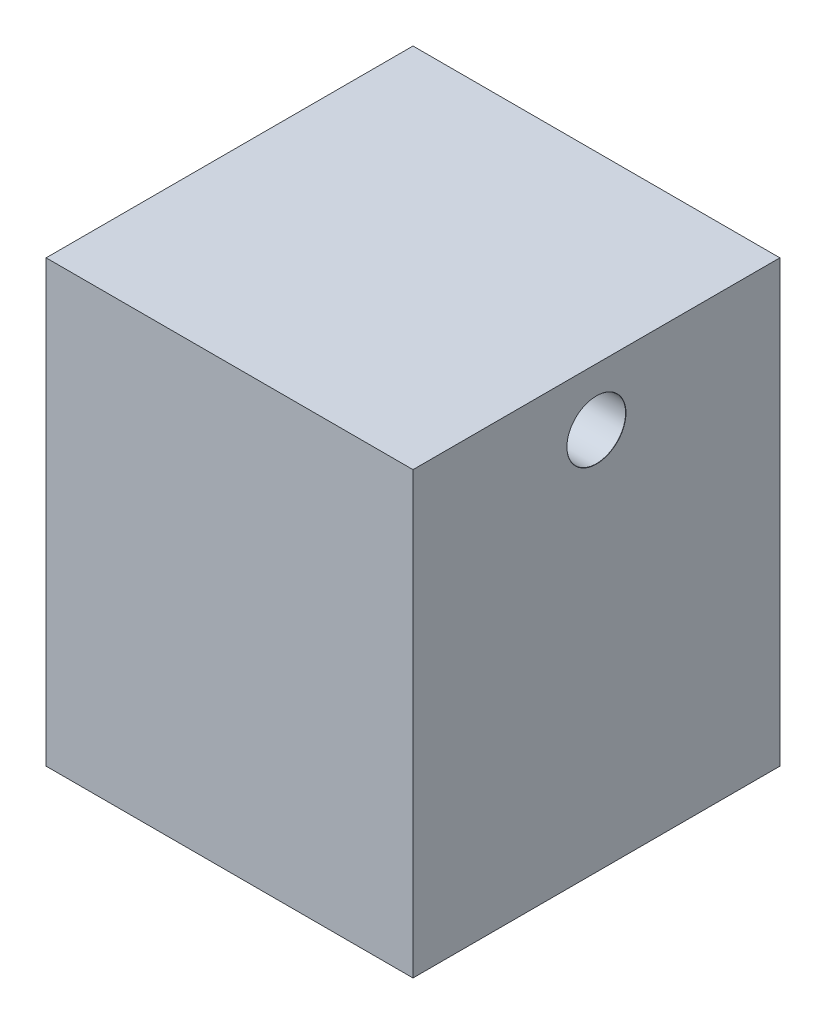
SolidWorks part; units mm, degrees
ref_plane "Front Plane" through (0, 0, 0) normal (0, 0, 1) x (1, 0, 0)
ref_plane "Top Plane" through (0, 0, 0) normal (0, 1, 0) x (1, 0, 0)
ref_plane "Right Plane" through (0, 0, 0) normal (1, 0, 0) x (0, 0, -1)
sketch "Sketch1" plane through (0, 0, 0) normal (0, 1, 0) x (1, 0, 0)
  line L5 (-25, -25) -> (25, -25)
  line L6 (-25, -25) -> (-25, 25)
  line L7 (-25, 25) -> (25, 25)
  line L8 (25, -25) -> (25, 25)
  line L9 (-25, -25) -> (25, 25) construction
  line L10 (-25, 25) -> (25, -25) construction
  point P0 (0, 0)
  dimension "D1" = 50
  dimension "D2" = 50
extrude "Boss-Extrude1" add sketch "Sketch1" along normal blind 60 contours L6 L5 L8 L7
hole_wizard "Ø8.0mm Dowel Hole1" positions "Sketch2" profile "Sketch3" hole size "Ø8.0" standard "ISO" end condition through all
sketch "Sketch2" plane through (25, 0, 0) normal (1, 0, 0) x (0, 0, -1)
  point P0 (0, 52.1841)
  point P2 (0, 52.1841)
sketch "Sketch3" plane through (25, 52.1841, 0) normal (0, 1, 0) x (0, 0, -1)
  line L0 (0, 0) -> (0, 50)
  line L1 (0, 50) -> (4, 50)
  line L2 (4, 50) -> (4, 0.025)
  line L3 (4, 0.025) -> (4.025, 0)
  line L5 (4.025, 0) -> (0, 0)
  line L6 (-4, 0.025) -> (-4.025, 0) construction
  line L11 (0, -6.35) -> (0, 107.95) construction
  dimension "Thru Hole Dia." = 8
  dimension "Thru Hole Depth" = 50
  dimension "Near C'Sink Dia." = 8.05
  dimension "Near C'Sink Angle" = 90
